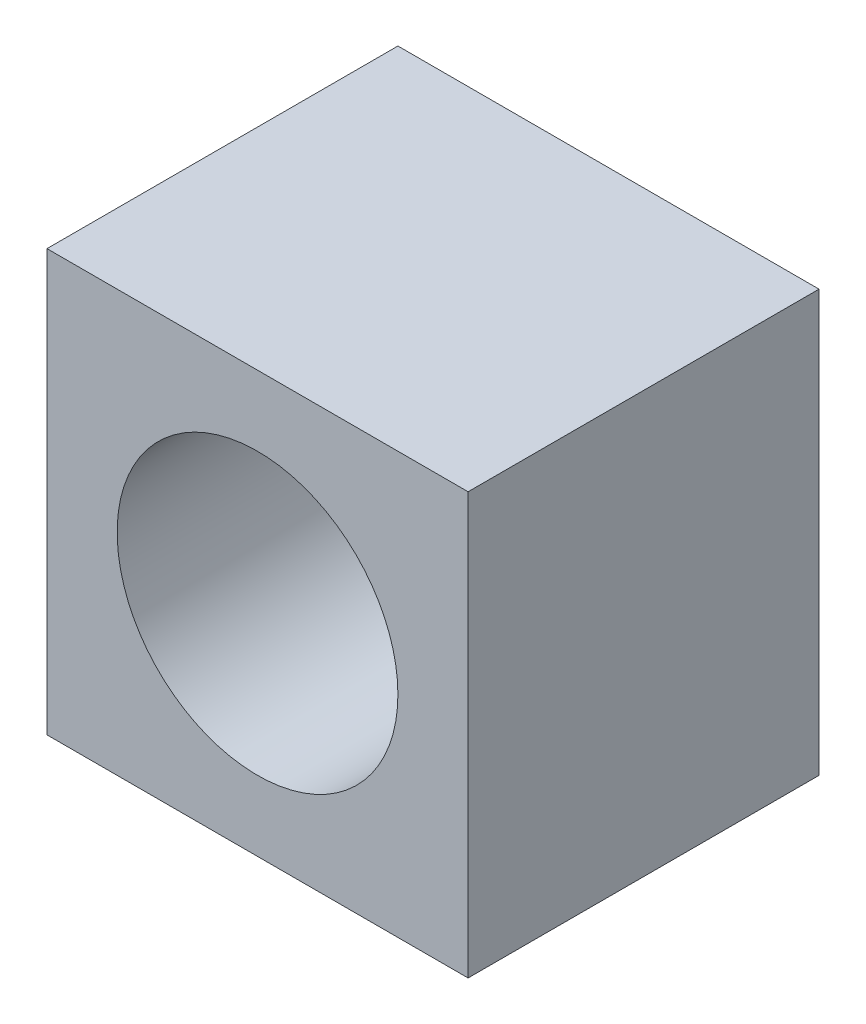
SolidWorks part; units mm, degrees
ref_plane "Front Plane" through (0, 0, 0) normal (0, 0, 1) x (1, 0, 0)
ref_plane "Top Plane" through (0, 0, 0) normal (0, 1, 0) x (1, 0, 0)
ref_plane "Right Plane" through (0, 0, 0) normal (1, 0, 0) x (0, 0, -1)
sketch "Sketch1" plane through (0, 0, 0) normal (0, 0, 1) x (1, 0, 0)
  line L5 (-6, 6) -> (6, 6)
  line L6 (-6, 6) -> (-6, -6)
  line L7 (-6, -6) -> (6, -6)
  line L8 (6, 6) -> (6, -6)
  line L9 (0, -6) -> (0, 6) construction
  line L10 (-6, 0) -> (6, 0) construction
  point P0 (0, 0)
  dimension "D1" = 12
  dimension "D2" = 12
extrude "Boss-Extrude2" add sketch "Sketch1" along normal blind 10
sketch "Sketch2" plane through (0, 0, 10) normal (0, 0, 1) x (1, 0, 0)
  circle A0 centre (0, 0) radius 4
  dimension "D1" = 8
extrude "Cut-Extrude1" cut sketch "Sketch2" against normal blind 8
